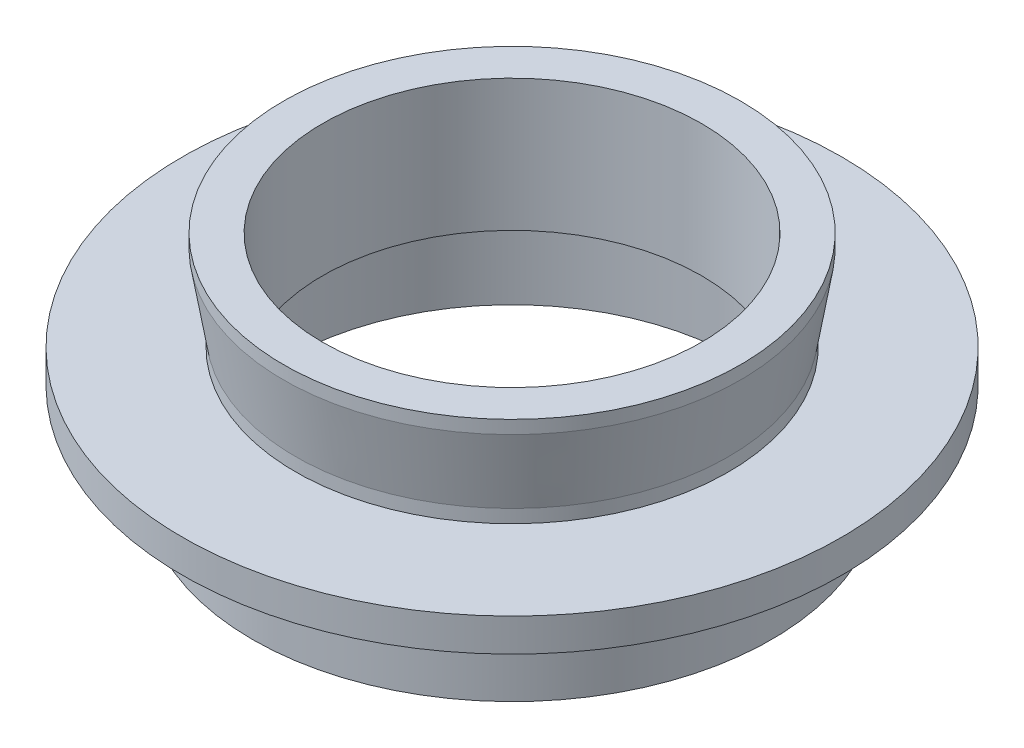
SolidWorks part; units mm, degrees
ref_plane "前视基准面" through (0, 0, 0) normal (0, 0, 1) x (1, 0, 0)
ref_plane "上视基准面" through (0, 0, 0) normal (0, 1, 0) x (1, 0, 0)
ref_plane "右视基准面" through (0, 0, 0) normal (1, 0, 0) x (0, 0, -1)
sketch "草图1" plane through (0, 0, 0) normal (0, 0, 1) x (1, 0, 0)
  line L0 (0, 0) -> (0, 73.2965) construction
  line L1 (-11.5, 5) -> (-11.5, 13)
  line L2 (-11.5, 13) -> (-13.865, 13)
  line L3 (-13.865, 13) -> (-13.865, 12.2)
  line L4 (-13.865, 12.2) -> (-13.135, 7.8)
  line L5 (-13.135, 7.8) -> (-13.135, 7)
  line L6 (-13.135, 7) -> (-20, 7)
  line L7 (-20, 7) -> (-20, 5)
  line L8 (-20, 5) -> (-15.75, 5)
  line L11 (-15.75, 5) -> (-15.75, -0.5)
  line L12 (-15.75, -0.5) -> (-13.75, -0.5)
  line L13 (-11.5, 5) -> (-14.5, 5)
  line L14 (-14.5, 5) -> (-14.5, 4)
  line L15 (-14.5, 4) -> (-13.75, 4)
  line L16 (-13.75, 4) -> (-13.75, -0.5)
  dimension "D1" = 11.5
  dimension "D2" = 13.865
  dimension "D3" = 13.135
  dimension "D4" = 15.75
  dimension "D5" = 0
  dimension "D6" = 13.5
  dimension "D7" = 6
  dimension "D8" = 2
  dimension "D9" = 13.75
  dimension "D10" = 0.8
  dimension "D11" = 0.8
  dimension "D13" = 20
  dimension "D14" = 1
  dimension "D15" = 14.5
revolve "旋转1" add sketch "草图1" angle 360 about L0
cosmetic thread "装饰螺纹线1" parameters "D1"=9, "D2"=24
cosmetic thread "装饰螺纹线2" parameters "D2"=28.5
